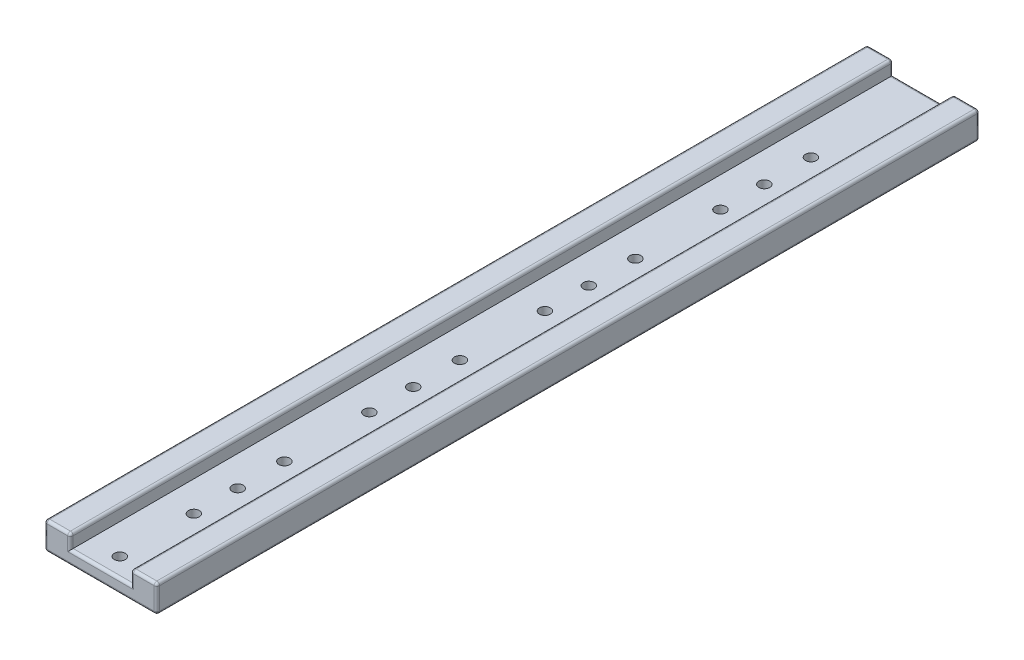
SolidWorks part; units mm, degrees
ref_plane "Front Plane" through (0, 0, 0) normal (0, 0, 1) x (1, 0, 0)
ref_plane "Top Plane" through (0, 0, 0) normal (0, 1, 0) x (1, 0, 0)
ref_plane "Right Plane" through (0, 0, 0) normal (1, 0, 0) x (0, 0, -1)
sketch "Sketch1" plane through (0, 0, 0) normal (0, 0, 1) x (1, 0, 0)
  line L0 (-11, 5) -> (-11, 0)
  line L1 (-20.5, -5) -> (20.5, -5)
  line L2 (-20.5, -5) -> (-20.5, 5)
  line L3 (-20.5, 5) -> (-11, 5)
  line L4 (20.5, -5) -> (20.5, 5)
  line L5 (-20.5, -5) -> (20.5, 5) construction
  line L6 (-20.5, 5) -> (20.5, -5) construction
  line L7 (-11, 0) -> (11, 0)
  line L8 (11, 0) -> (11, 5)
  line L9 (11, 5) -> (20.5, 5)
  point P0 (0, 0)
  dimension "D1" = 41
  dimension "D2" = 10
  dimension "D3" = 22
  dimension "D4" = 9.5
extrude "Boss-Extrude1" add sketch "Sketch1" along normal blind 300
ref_plane "Plane1" through (0, 0, 150) normal (0, 0, -1) x (-1, 0, 0)
sketch "Sketch2" plane through (0, -5, 0) normal (0, -1, 0) x (1, 0, 0)
  line L0 (20.5, 300) -> (20.5, 0) construction
  line L1 (-20.5, 300) -> (-20.5, 0) construction
  line L2 (-20.5, 300) -> (20.5, 300) construction
  circle A0 centre (-14.5, 293) radius 2
  circle A1 centre (0, 293) radius 2
  circle A2 centre (14.5, 293) radius 2
  circle A3 centre (0, 266) radius 2
  circle A4 centre (0, 250) radius 2
  circle A5 centre (0, 233) radius 2
  circle A6 centre (0, 169) radius 2
  circle A7 centre (0, 105) radius 2
  circle A8 centre (0, 186) radius 2
  circle A9 centre (0, 122) radius 2
  circle A10 centre (0, 202) radius 2
  circle A11 centre (0, 138) radius 2
  circle A13 centre (0, 74) radius 2
  circle A14 centre (0, 58) radius 2
  circle A15 centre (0, 41) radius 2
  dimension "D1" = 4
  dimension "D2" = 4
  dimension "D3" = 4
  dimension "D8" = 4
  dimension "D9" = 4
  dimension "D10" = 4
  dimension "D12" = 50
  dimension "D13" = 67
  dimension "D4" = 6
  dimension "D5" = 20.5
  dimension "D6" = 6
  dimension "D7" = 7
  dimension "D11" = 34
  dimension "D14" = 4
  dimension "D15" = 4
  dimension "D16" = 4
extrude "Cut-Extrude1" cut sketch "Sketch2" against normal blind 5
fillet "Fillet1" radius 1 6 edges at (11, 5, 150) (-11, 5, 150) (20.5, -5, 150) (-20.5, -5, 150) (-20.5, 5, 150) (20.5, 5, 150)
fillet "Fillet2" radius 1 28 edges at (0, 0, 0) (-11, 2, 0) (-11.2929, 4.7071, 0) (-15.75, 5, 0) (-20.2071, 4.7071, 0) (-20.5, 0, 0) (-20.2071, -4.7071, 0) (0, -5, 0) (20.2071, -4.7071, 0) (20.5, 0, 0) (20.2071, 4.7071, 0) (15.75, 5, 0) (11.2929, 4.7071, 0) (11, 2, 0) (20.2071, 4.7071, 300) (20.5, 0, 300) (20.2071, -4.7071, 300) (0, -5, 300) (-20.2071, -4.7071, 300) (-20.5, 0, 300) (-20.2071, 4.7071, 300) (-15.75, 5, 300) (-11.2929, 4.7071, 300) (-11, 2, 300) (0, 0, 300) (11, 2, 300) (11.2929, 4.7071, 300) (15.75, 5, 300)
